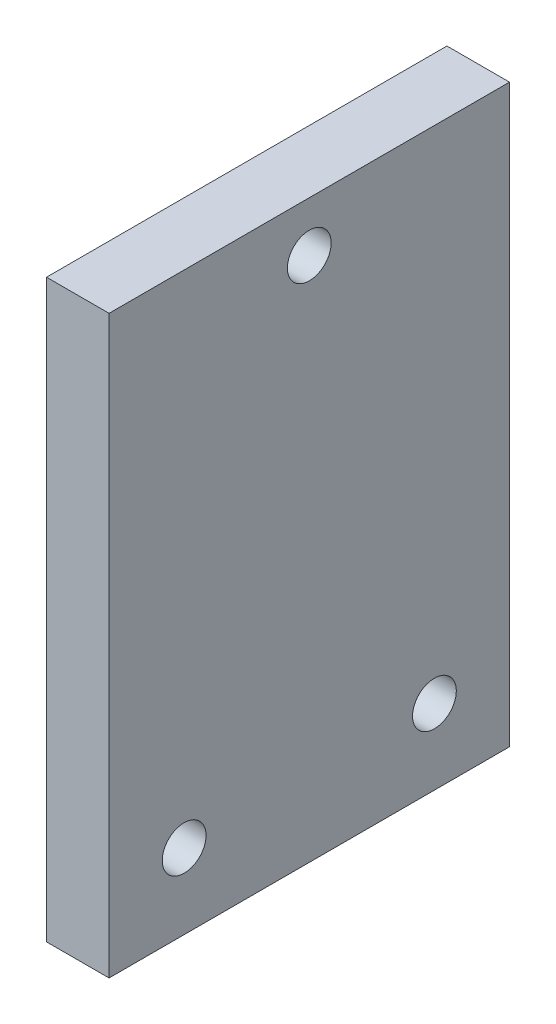
SolidWorks part; units mm, degrees
ref_plane "Front Plane" through (0, 0, 0) normal (0, 0, 1) x (1, 0, 0)
ref_plane "Top Plane" through (0, 0, 0) normal (0, 1, 0) x (1, 0, 0)
ref_plane "Right Plane" through (0, 0, 0) normal (1, 0, 0) x (0, 0, -1)
sketch "Sketch1" plane through (0, 0, 0) normal (0, 1, 0) x (1, 0, 0)
  line L1 (0, 0) -> (55, 0)
  line L2 (0, 0) -> (0, 32)
  line L3 (0, 32) -> (55, 32)
  line L4 (55, 0) -> (55, 32)
  dimension "D1" = 32
  dimension "D2" = 55
extrude "Boss-Extrude1" add sketch "Sketch1" along normal blind 46
sketch "Sketch2" plane through (0, 0, 0) normal (0, -1, 0) x (1, 0, 0)
  line L0 (0, 0) -> (55, 0) construction
  line L1 (5, 0) -> (50, 0)
  line L2 (5, 0) -> (5, -32)
  line L3 (5, -32) -> (50, -32)
  line L4 (50, 0) -> (50, -32)
  line L5 (55, -32) -> (0, -32) construction
  line L6 (0, -32) -> (0, 0) construction
  line L7 (55, 0) -> (55, -32) construction
  dimension "D1" = 5
  dimension "D2" = 5
extrude "Cut-Extrude1" cut sketch "Sketch2" against normal blind 45
sketch "Sketch3" plane through (0, 46, 0) normal (0, 1, 0) x (1, 0, 0)
  line L0 (55, 32) -> (0, 32) construction
  line L1 (55, 0) -> (55, 32) construction
  circle A0 centre (43.5, 26) radius 1.75
  circle A1 centre (43.5, 6) radius 1.75
  circle A2 centre (11.5, 26) radius 1.75
  circle A3 centre (11.5, 6) radius 1.75
  dimension "D1" = 3.5
  dimension "D2" = 20
  dimension "D3" = 20
  dimension "D4" = 32
  dimension "D5" = 32
  dimension "D6" = 6
  dimension "D7" = 11.5
extrude "Cut-Extrude2" cut sketch "Sketch3" against normal through all
sketch "Sketch4" plane through (55, 0, 0) normal (1, 0, 0) x (0, 0, -1)
  line L0 (0, 46) -> (32, 46) construction
  line L1 (0, 46) -> (0, 0) construction
  circle A0 centre (6, 6) radius 1.75
  circle A1 centre (26, 6) radius 1.75
  circle A2 centre (16, 42) radius 1.75
  dimension "D1" = 3.5
  dimension "D2" = 3.5
  dimension "D6" = 3.5
  dimension "D3" = 20
  dimension "D4" = 40
  dimension "D5" = 6
  dimension "D7" = 4
  dimension "D8" = 16
extrude "Cut-Extrude3" cut sketch "Sketch4" against normal through all
sketch "Sketch5" plane through (50, 0, 0) normal (-1, 0, 0) x (0, 0, 1)
  line L0 (-30, 10) -> (-28.9, 10)
  line L1 (-32, 45) -> (-30.9, 45)
  line L2 (-32, 45) -> (-32, 10)
  line L3 (-32, 10) -> (-30.9, 10)
  line L4 (-30.9, 45) -> (-30.9, 10)
  line L5 (-28.9, 45) -> (-28.9, 10)
  line L6 (-30, 45) -> (-30, 10)
  line L7 (-30, 45) -> (-28.9, 45)
  line L8 (-28, 10) -> (-26.9, 10)
  line L9 (-26.9, 45) -> (-26.9, 10)
  line L10 (-28, 45) -> (-28, 10)
  line L11 (-28, 45) -> (-26.9, 45)
  line L12 (-26, 10) -> (-24.9, 10)
  line L13 (-24.9, 45) -> (-24.9, 10)
  line L14 (-26, 45) -> (-26, 10)
  line L15 (-26, 45) -> (-24.9, 45)
  line L16 (-24, 10) -> (-22.9, 10)
  line L17 (-22.9, 45) -> (-22.9, 10)
  line L18 (-24, 45) -> (-24, 10)
  line L19 (-24, 45) -> (-22.9, 45)
  line L20 (-22, 10) -> (-20.9, 10)
  line L21 (-20.9, 45) -> (-20.9, 10)
  line L22 (-22, 45) -> (-22, 10)
  line L23 (-22, 45) -> (-20.9, 45)
  line L24 (-20, 10) -> (-18.9, 10)
  line L25 (-18.9, 45) -> (-18.9, 10)
  line L26 (-20, 45) -> (-20, 10)
  line L27 (-20, 45) -> (-18.9, 45)
  line L28 (-18, 10) -> (-16.9, 10)
  line L29 (-16.9, 45) -> (-16.9, 10)
  line L30 (-18, 45) -> (-18, 10)
  line L31 (-18, 45) -> (-16.9, 45)
  line L32 (-16, 10) -> (-14.9, 10)
  line L33 (-14.9, 45) -> (-14.9, 10)
  line L34 (-16, 45) -> (-16, 10)
  line L35 (-16, 45) -> (-14.9, 45)
  line L36 (-14, 10) -> (-12.9, 10)
  line L37 (-12.9, 45) -> (-12.9, 10)
  line L38 (-14, 45) -> (-14, 10)
  line L39 (-14, 45) -> (-12.9, 45)
  line L40 (-12, 10) -> (-10.9, 10)
  line L41 (-10.9, 45) -> (-10.9, 10)
  line L42 (-12, 45) -> (-12, 10)
  line L43 (-12, 45) -> (-10.9, 45)
  line L44 (-10, 10) -> (-8.9, 10)
  line L45 (-8.9, 45) -> (-8.9, 10)
  line L46 (-10, 45) -> (-10, 10)
  line L47 (-10, 45) -> (-8.9, 45)
  line L48 (-8, 10) -> (-6.9, 10)
  line L49 (-6.9, 45) -> (-6.9, 10)
  line L50 (-8, 45) -> (-8, 10)
  line L51 (-8, 45) -> (-6.9, 45)
  line L52 (-6, 10) -> (-4.9, 10)
  line L53 (-4.9, 45) -> (-4.9, 10)
  line L54 (-6, 45) -> (-6, 10)
  line L55 (-6, 45) -> (-4.9, 45)
  line L56 (-4, 10) -> (-2.9, 10)
  line L57 (-2.9, 45) -> (-2.9, 10)
  line L58 (-4, 45) -> (-4, 10)
  line L59 (-4, 45) -> (-2.9, 45)
  line L60 (-2, 10) -> (-0.9, 10)
  line L61 (-0.9, 45) -> (-0.9, 10)
  line L62 (-2, 45) -> (-2, 10)
  line L63 (-2, 45) -> (-0.9, 45)
  line L64 (0, 10) -> (1.1, 10)
  line L65 (1.1, 45) -> (1.1, 10)
  line L66 (0, 45) -> (0, 10)
  line L67 (0, 45) -> (1.1, 45)
  dimension "D1" = 35
  dimension "D2" = 1.1
  dimension "D3" = 17
extrude "Cut-Extrude4" cut sketch "Sketch5" against normal blind 1.2
sketch "Sketch7" plane through (0, 0, 0) normal (-1, 0, 0) x (0, 0, 1)
  line L0 (-32, 46) -> (-32, 0) construction
  line L1 (-32, 0) -> (0, 0)
  line L2 (-32, 0) -> (-32, 46)
  line L3 (-32, 46) -> (0, 46)
  line L4 (0, 0) -> (0, 46)
  line L5 (-32, 0) -> (0, 0) construction
extrude "Cut-Extrude5" cut sketch "Sketch7" against normal blind 50
